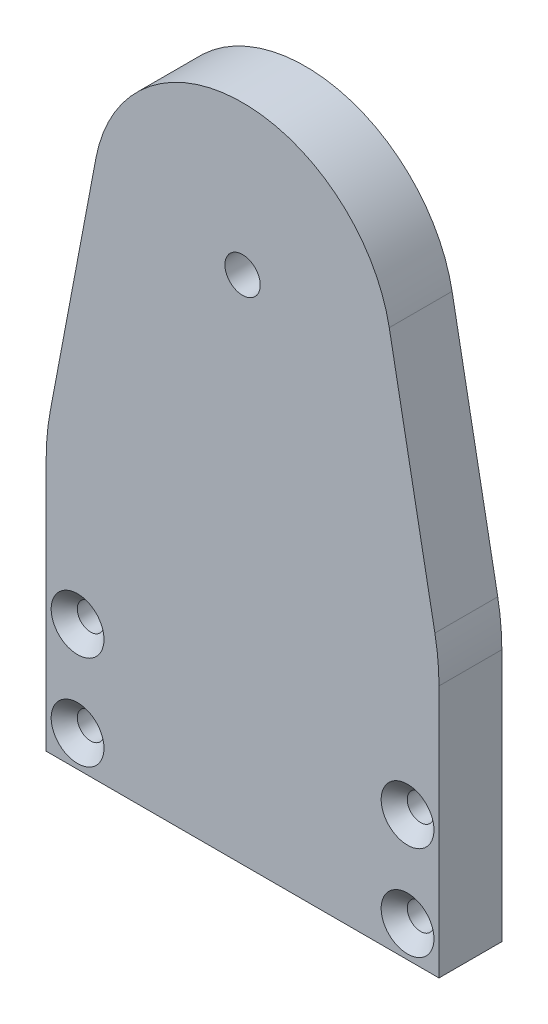
SolidWorks part; units mm, degrees
ref_plane "정면" through (0, 0, 0) normal (0, 0, 1) x (1, 0, 0)
ref_plane "윗면" through (0, 0, 0) normal (0, 1, 0) x (1, 0, 0)
ref_plane "우측면" through (0, 0, 0) normal (1, 0, 0) x (0, 0, -1)
sketch "스케치1" plane through (0, 0, 0) normal (0, 0, 1) x (1, 0, 0)
  line L0 (0, 0) -> (50, 0)
  line L1 (50, 0) -> (50, 35)
  line L2 (50, 35) -> (43.6701, 68.5251)
  line L3 (25, 0) -> (25, 65) construction
  line L4 (0, 35) -> (6.3299, 68.5251)
  line L5 (0, 0) -> (0, 35)
  circle A0 centre (25, 65) radius 19
  dimension "D1" = 38
  dimension "D3" = 65
  dimension "D4" = 50
  dimension "D5" = 35
extrude "보스-돌출1" add sketch "스케치1" along normal blind 8
fillet "필렛1" radius 30 2 edges at (0, 35, 4) (50, 35, 4)
sketch "스케치2" plane through (0, 0, 0) normal (0, 0, -1) x (-1, 0, 0)
  arc A0 (-6.3299, 68.5251) -> (-43.6701, 68.5251) centre (-25, 65) ccw construction
  arc A1 (-6.3299, 68.5251) -> (-43.6701, 68.5251) centre (-25, 65) ccw
  circle A2 centre (-25, 65) radius 14
  dimension "D1" = 28
extrude "컷-돌출1" cut sketch "스케치2" against normal blind 4 contours A2
hole_wizard "M4 여유 구멍1" positions "스케치3" profile "스케치4" hole size "M4" standard "ISO" end condition through all
sketch "스케치3" plane through (0, 0, 8) normal (0, 0, 1) x (1, 0, 0)
  point P0 (25, 65)
sketch "스케치4" plane through (25, 65, 8) normal (1, 0, 0) x (0, -1, 0)
  line L0 (0, 0) -> (0, 8)
  line L1 (0, 8) -> (2.25, 8)
  line L2 (2.25, 8) -> (2.25, 0)
  line L5 (2.25, 0) -> (0, 0)
  line L11 (0, -6.35) -> (0, 107.95) construction
  dimension "관통 구멍 지름" = 4.5
  dimension "관통 구멍 깊이" = 8
hole_wizard "M3 육각 소켓 접시 머리 캡 나사용 카운터싱크1" positions "스케치5" profile "스케치6" countersink size "M3" standard "ISO" end condition up to next
sketch "스케치5" plane through (0, 0, 8) normal (0, 0, 1) x (1, 0, 0)
  line L5 (4, 16) -> (46, 16)
  line L6 (4, 16) -> (4, 4)
  line L7 (4, 4) -> (46, 4)
  line L8 (46, 16) -> (46, 4)
  line L9 (0, 0) -> (0, 32.1927) construction
  line L10 (0, 0) -> (50, 0) construction
  line L11 (50, 0) -> (50, 32.1927) construction
  point P0 (4, 16)
  point P2 (4, 4)
  point P4 (46, 4)
  point P6 (46, 16)
  dimension "D1" = 4
  dimension "D2" = 4
  dimension "D3" = 4
  dimension "D4" = 12
sketch "스케치6" plane through (4, 16, 8) normal (1, 0, 0) x (0, -1, 0)
  line L0 (0, 0) -> (0, 8)
  line L1 (0, 8) -> (1.7, 8)
  line L2 (1.7, 8) -> (1.7, 1.66)
  line L3 (1.7, 1.66) -> (3.36, 0)
  line L5 (3.36, 0) -> (0, 0)
  line L6 (-1.7, 1.66) -> (-3.36, 0) construction
  line L11 (0, -6.35) -> (0, 107.95) construction
  dimension "관통 구멍 지름" = 3.4
  dimension "관통 구멍 깊이" = 8
  dimension "표면 카운터싱크 지름" = 6.72
  dimension "표면 카운터싱크 각도" = 90
hole_wizard "M3 나사 구멍1" positions "스케치7" profile "스케치8" tap size "M3" standard "ISO"
sketch "스케치7" plane through (0, 0, 0) normal (0, -1, 0) x (-1, 0, 0)
  line L0 (-38, -4) -> (-12, -4)
  line L2 (-50, -8) -> (-50, 0) construction
  line L3 (0, -8) -> (0, 0) construction
  point P0 (-38, -4)
  point P2 (-12, -4)
  point P13 (-50, -4)
  dimension "D1" = 12
  dimension "D2" = 12
sketch "스케치8" plane through (38, 0, 4) normal (1, 0, 0) x (0, 0, -1)
  line L0 (0, 0) -> (0, 9.2511)
  line L1 (0, 9.2511) -> (1.25, 8.5)
  line L2 (1.25, 8.5) -> (1.25, 0)
  line L5 (1.25, 0) -> (0, 0)
  line L10 (0, 9.2511) -> (-1.25, 8.5) construction
  line L11 (0, -6.35) -> (0, 107.95) construction
  dimension "탭 드릴 지름" = 2.5
  dimension "탭 드릴 깊이" = 8.5
  dimension "드릴 각도" = 118
cosmetic thread "구멍 나사산1" parameters "D1"=6, "D2"=3
cosmetic thread "구멍 나사산2" parameters "D1"=6, "D2"=3
